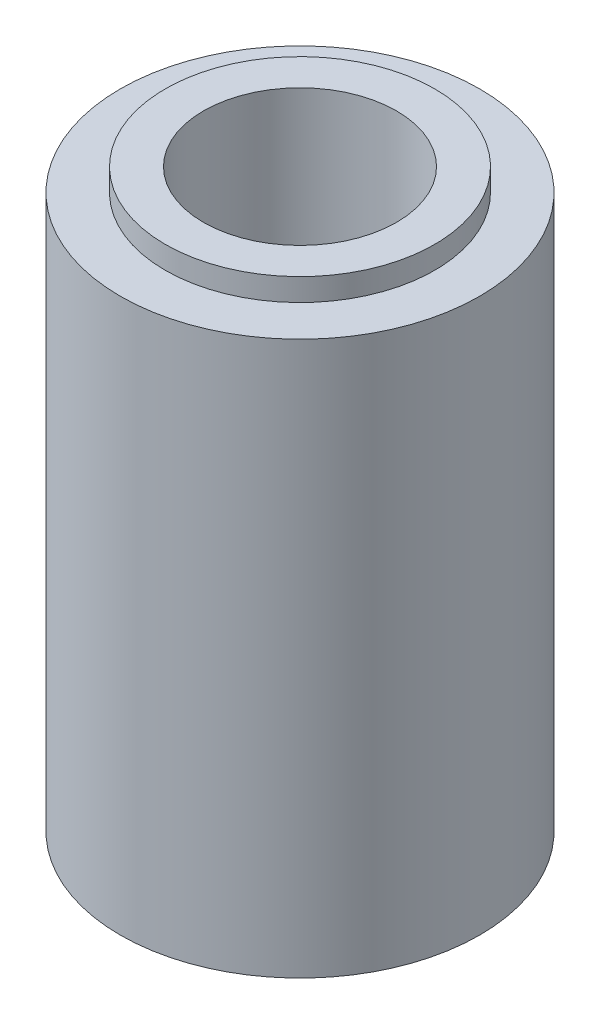
SolidWorks part; units mm, degrees
ref_plane "Front Plane" through (0, 0, 0) normal (0, 0, 1) x (1, 0, 0)
ref_plane "Top Plane" through (0, 0, 0) normal (0, 1, 0) x (1, 0, 0)
ref_plane "Right Plane" through (0, 0, 0) normal (1, 0, 0) x (0, 0, -1)
sketch "Sketch1" plane through (0, 0, 0) normal (0, 1, 0) x (1, 0, 0)
  circle A0 centre (0, 0) radius 4
  dimension "D1" = 8
extrude "Boss-Extrude1" add sketch "Sketch1" along normal blind 12.82
sketch "Sketch2" plane through (0, 12.82, 0) normal (0, 1, 0) x (1, 0, 0)
  circle A0 centre (0, 0) radius 3
  dimension "D1" = 6
extrude "Cut-Extrude1" cut sketch "Sketch2" against normal blind 0.5 flip side to cut
hole_wizard "M4 Clearance Hole1" positions "Sketch3" profile "Sketch4" hole size "M4" standard "ANSI Metric" end condition through all
sketch "Sketch3" plane through (0, 12.82, 0) normal (0, 1, 0) x (1, 0, 0)
  point P0 (0, 0)
sketch "Sketch4" plane through (0, 12.82, 0) normal (1, 0, 0) x (0, 0, 1)
  line L0 (0, 0) -> (0, 12.82)
  line L1 (0, 12.82) -> (2.15, 12.82)
  line L2 (2.15, 12.82) -> (2.15, 0)
  line L5 (2.15, 0) -> (0, 0)
  line L11 (0, -6.35) -> (0, 107.95) construction
  dimension "Thru Hole Dia." = 4.3
  dimension "Thru Hole Depth" = 12.82
